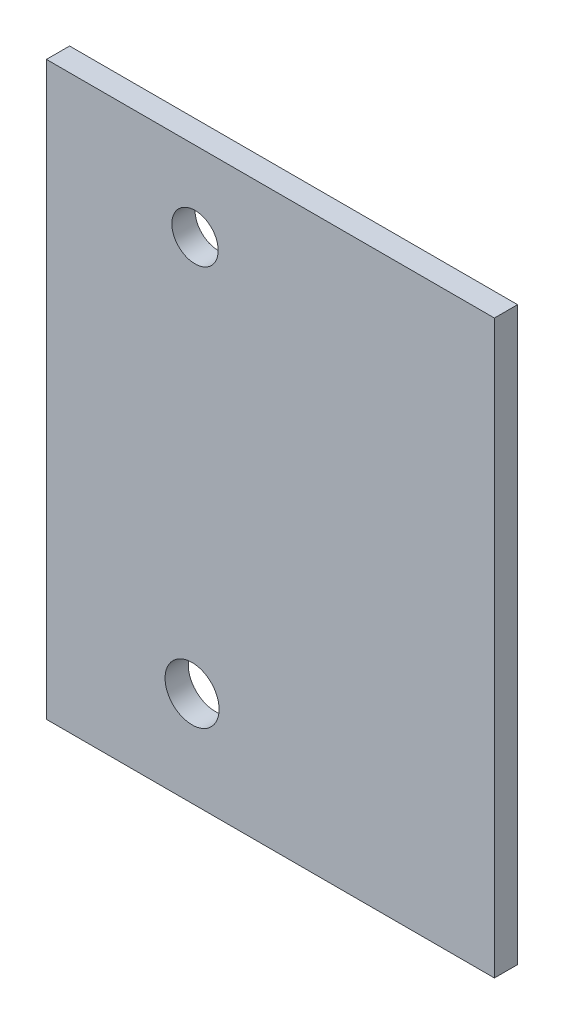
SolidWorks part; units mm, degrees
ref_plane "Спереди (XY) " through (0, 0, 0) normal (0, 0, 1) x (1, 0, 0)
ref_plane "Сверху (XZ)" through (0, 0, 0) normal (0, 1, 0) x (1, 0, 0)
ref_plane "Справа (ZY)" through (0, 0, 0) normal (1, 0, 0) x (0, 0, -1)
sketch "Эскиз1" plane through (0, 0, 0) normal (0, 0, 1) x (1, 0, 0)
  line L1 (0, 0) -> (29, 0)
  line L2 (0, 0) -> (0, 37)
  line L3 (0, 37) -> (29, 37)
  line L4 (29, 0) -> (29, 37)
  dimension "D1" = 37
  dimension "D2" = 29
extrude "Бобышка-Вытянуть1" add sketch "Эскиз1" along normal blind 1.5
sketch "Эскиз2" plane through (0, 0, 1.5) normal (0, 0, 1) x (1, 0, 0)
  line L3 (10.89, 31.845) -> (8.35, 31.845) construction
  circle A0 centre (9.62, 31.845) radius 1.5
  circle A1 centre (9.4291, 6.154) radius 1.75
  point P2 (9.62, 31.845)
  point P4 (13.4474, 34.5)
  dimension "D1" = 3
  dimension "D2" = 3.5
extrude "Вырез-Вытянуть1" cut sketch "Эскиз2" against normal through all
equation "\"Mass_int\"= int ( ( \"SW-Масса\" + 0.005 ) * 100 ) / 100"
